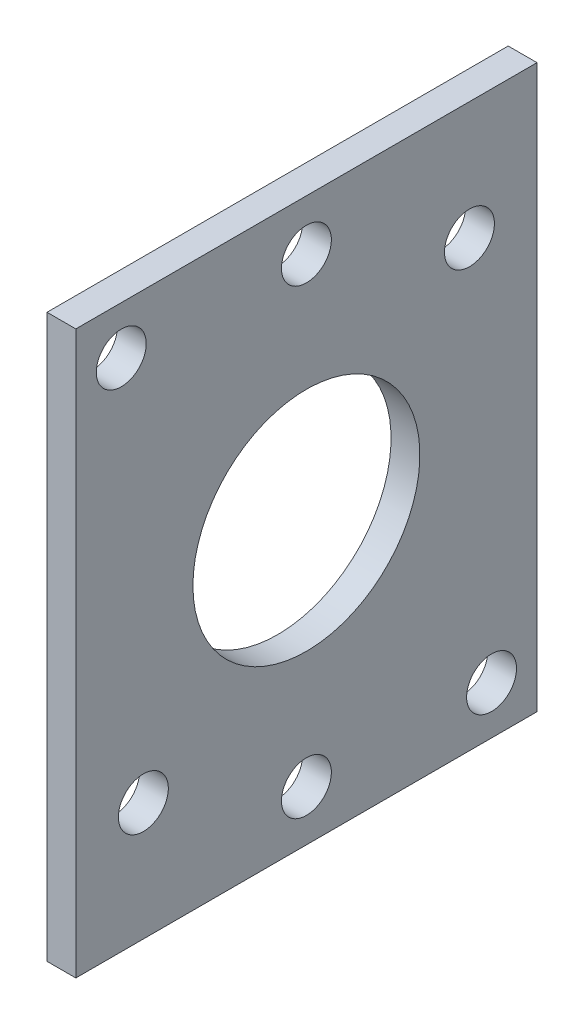
SolidWorks part; units mm, degrees
ref_plane "Front Plane" through (0, 0, 0) normal (0, 0, 1) x (1, 0, 0)
ref_plane "Top Plane" through (0, 0, 0) normal (0, 1, 0) x (1, 0, 0)
ref_plane "Right Plane" through (0, 0, 0) normal (1, 0, 0) x (0, 0, -1)
sketch "Sketch1" plane through (0, 0, 0) normal (1, 0, 0) x (0, 0, -1)
  line L45 (0, 0) -> (50.8, 0)
  line L46 (0, 0) -> (0, 61.92)
  line L47 (0, 61.92) -> (50.8, 61.92)
  line L48 (50.8, 0) -> (50.8, 61.92)
  dimension "D1" = 61.92
  dimension "D2" = 50.8
extrude "Boss-Extrude2" add sketch "Sketch1" along normal blind 3.175
sketch "Sketch2" plane through (0, 0, 0) normal (-1, 0, 0) x (0, 0, 1)
  circle A4 centre (-25.3997, 30.96) radius 12.5 construction
  circle A5 centre (-43.3599, 48.9208) radius 2.75 construction
  circle A12 centre (-25.3997, 56.36) radius 2.75 construction
  circle A14 centre (-5.0045, 56.6481) radius 2.75 construction
  circle A15 centre (-25.3997, 5.5607) radius 2.75 construction
  circle A16 centre (-45.7955, 5.2725) radius 2.75 construction
  circle A17 centre (-7.4395, 13.0002) radius 2.75 construction
  circle A18 centre (-25.3997, 30.96) radius 12.5
  circle A19 centre (-43.3599, 48.9208) radius 2.75
  circle A20 centre (-25.3997, 56.36) radius 2.75
  circle A21 centre (-5.0045, 56.6481) radius 2.75
  circle A22 centre (-25.3997, 5.5607) radius 2.75
  circle A23 centre (-45.7955, 5.2725) radius 2.75
  circle A24 centre (-7.4395, 13.0002) radius 2.75
extrude "Cut-Extrude1" cut sketch "Sketch2" against normal through all
